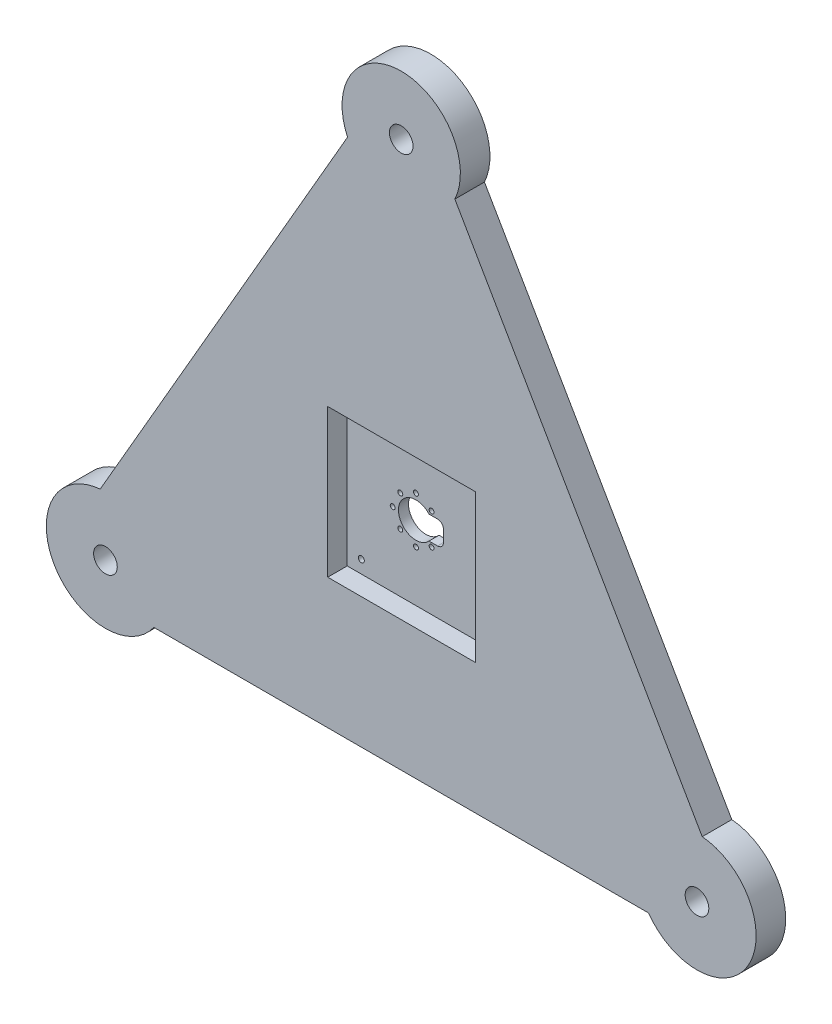
SolidWorks part; units mm, degrees
material "6061-T6 (SS)"
ref_plane "Front Plane" through (0, 0, 0) normal (0, 0, 1) x (1, 0, 0)
ref_plane "Top Plane" through (0, 0, 0) normal (0, 1, 0) x (1, 0, 0)
ref_plane "Right Plane" through (0, 0, 0) normal (1, 0, 0) x (0, 0, -1)
sketch "Sketch1" plane through (0, 0, 0) normal (0, 0, 1) x (1, 0, 0)
  line L1 (0, 175.8553) -> (-152.2952, -87.9277)
  line L2 (-152.2952, -87.9277) -> (152.2952, -87.9277)
  line L3 (152.2952, -87.9277) -> (0, 175.8553)
  line L4 (0, 146.647) -> (-127, -73.3235)
  line L5 (-127, -73.3235) -> (127, -73.3235)
  line L6 (127, -73.3235) -> (0, 146.647)
  line L7 (-127, -73.3235) -> (-124.46, -68.9241)
  line L8 (-127, -73.3235) -> (-121.92, -73.3235)
  circle A0 centre (0, 0) radius 87.9277 construction
  circle A1 centre (0, 0) radius 73.3235 construction
  circle A2 centre (0, 146.647) radius 5.08
  circle A3 centre (-127, -73.3235) radius 5.08
  circle A4 centre (127, -73.3235) radius 5.08
  circle A5 centre (0, 146.647) radius 25.4
  circle A6 centre (127, -73.3235) radius 25.4
  circle A7 centre (-127, -73.3235) radius 25.4
  circle A8 centre (-127, -73.3235) radius 5.08
extrude "Boss-Extrude9" add sketch "Sketch1" along normal blind 12.7 contours L3 A6 L6 A4 L5 L2 | L3 A6 | L2 A6 | L4 A7 L1 L2 L5 A3 | L1 A7 | L2 A7 | A7 L2 A6 L5 | A7 L4 A5 L1 | A6 L3 A5 L6 | L3 A5 L1 L4 A2 L6 | L3 A5 | L1 A5 | L4 A5 L6 A2
sketch "Sketch2" plane through (0, 0, 12.7) normal (0, 0, 1) x (1, 0, 0)
  circle A0 centre (127, -73.3235) radius 5.08
  circle A1 centre (0, 146.647) radius 5.08
extrude "Cut-Extrude1" cut sketch "Sketch2" against normal through all both and the other way through all contours A0
sketch "Sketch4" plane through (0, 0, 12.7) normal (0, 0, 1) x (1, 0, 0)
  circle A0 centre (0, 146.647) radius 5.08
extrude "Cut-Extrude3" cut sketch "Sketch4" against normal through all
sketch "Sketch6" plane through (0, 0, 12.7) normal (0, 0, 1) x (1, 0, 0)
  line L1 (-31.5586, 31.5586) -> (31.9414, 31.5586)
  line L2 (-31.5586, 31.5586) -> (-31.5586, -31.9414)
  line L3 (-31.5586, -31.9414) -> (31.9414, -31.9414)
  line L4 (31.9414, 31.5586) -> (31.9414, -31.9414)
  line L5 (-31.5586, 31.5586) -> (31.9414, -31.9414) construction
  line L6 (-31.5586, -31.9414) -> (26.0398, 26.3556) construction
  point P0 (0, 0)
extrude "Cut-Extrude10" cut sketch "Sketch6" against normal blind 8.382 contours L2 L1 L4 L3
sketch "Sketch8" plane through (0, 0, 4.318) normal (0, 0, 1) x (1, 0, 0)
  circle A4 centre (-25.5113, -26.4093) radius 1.2954
  circle A5 centre (-25.5113, 26.8032) radius 1.2954
  circle A6 centre (27.2309, 26.8032) radius 1.2954
  circle A7 centre (27.2309, -26.4093) radius 1.2954
extrude "Cut-Extrude13" cut sketch "Sketch8" against normal through all
sketch "Sketch20" plane through (0, 0, 4.318) normal (0, 0, 1) x (1, 0, 0)
  circle A0 centre (4.6711, 6.5929) radius 1.0455
  circle A1 centre (-2.0489, 9.8729) radius 1.05
  circle A2 centre (-8.7689, 6.5929) radius 1.0531
  circle A3 centre (-12.0489, -0.1271) radius 1.0497
  circle A4 centre (-2.0489, -10.1271) radius 1.0604
  circle A5 centre (-8.7689, -6.8471) radius 1.05
  circle A6 centre (4.6711, -6.8471) radius 1.0414
extrude "Cut-Extrude14" cut sketch "Sketch20" against normal through all contours A3 | A5 | A4 | A6 | A0 | A1 | A2
sketch "Sketch22" plane through (0, 0, 11.7422) normal (0, 0, 1) x (1, 0, 0)
  line L1 (3.5413, -5.1271) -> (7.2151, -5.1271)
  line L2 (3.5413, -5.1271) -> (3.5413, 4.8811)
  line L3 (3.5413, 4.8811) -> (7.2151, 4.8811)
  line L4 (9.7551, -2.5871) -> (9.7551, 2.3411)
  circle A0 centre (-2.0542, -0.1319) radius 7.5071
  arc A1 (7.2151, -5.1271) -> (9.7551, -2.5871) centre (7.2151, -2.5871) ccw
  arc A2 (9.7551, 2.3411) -> (7.2151, 4.8811) centre (7.2151, 2.3411) ccw
  dimension "D1" = 2.54
extrude "Cut-Extrude15" cut sketch "Sketch22" against normal through all
sketch "Sketch23" plane through (0, 0, 12.7) normal (0, 0, 1) x (1, 0, 0)
  circle A0 centre (-126.9054, -73.3294) radius 10.16
  circle A1 centre (-126.9054, -73.3294) radius 5.08
sketch "Sketch24" plane through (0, 0, 12.7) normal (0, 0, 1) x (1, 0, 0)
  circle A0 centre (126.9679, -73.3017) radius 10.1988
  circle A1 centre (126.9679, -73.3017) radius 5.08
sketch "Sketch25" plane through (0, 0, 12.7) normal (0, 0, 1) x (1, 0, 0)
  circle A0 centre (0.0818, 146.6595) radius 10.0772
  circle A1 centre (0.0818, 146.6595) radius 5.08
sketch "Sketch26" plane through (0, 0, 12.7) normal (0, 0, 1) x (1, 0, 0)
  circle A0 centre (-127, -73.3235) radius 5.08
extrude "Cut-Extrude16" cut sketch "Sketch26" against normal through all both and the other way through all
